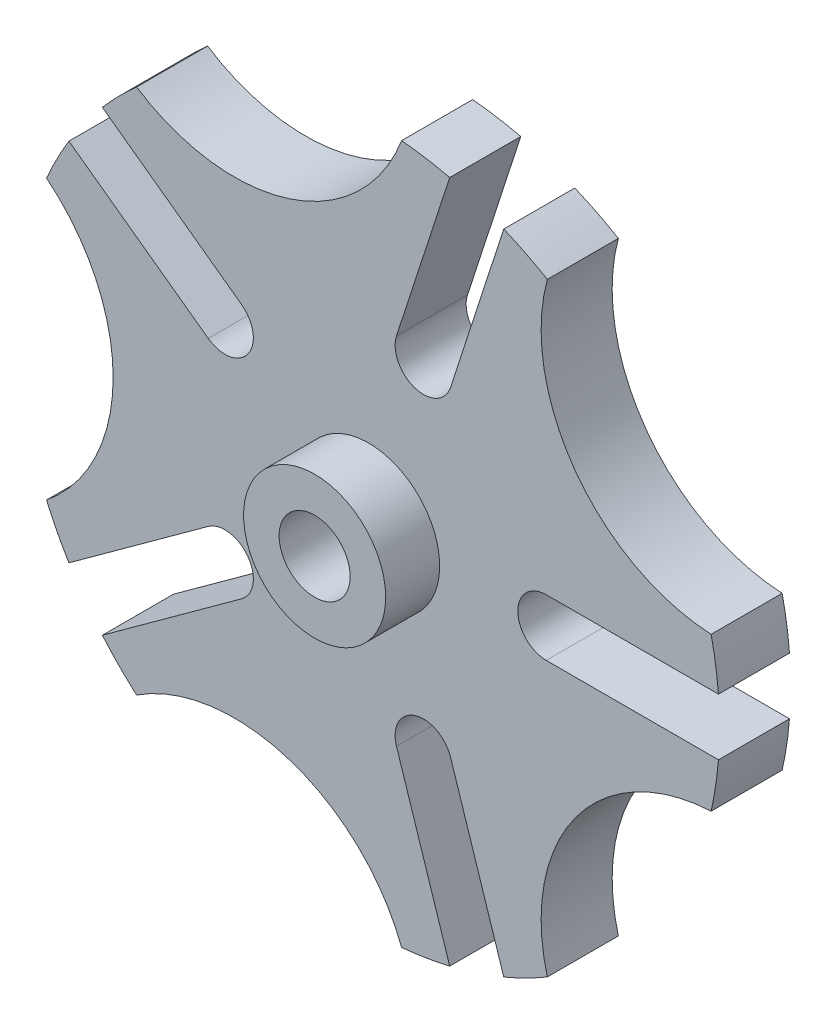
SolidWorks part; units mm, degrees
ref_plane "Front Plane" through (0, 0, 0) normal (0, 0, 1) x (1, 0, 0)
ref_plane "Top Plane" through (0, 0, 0) normal (0, 1, 0) x (1, 0, 0)
ref_plane "Right Plane" through (0, 0, 0) normal (1, 0, 0) x (0, 0, -1)
sketch "Sketch2" plane through (0, 0, 0) normal (0, 0, 1) x (1, 0, 0)
  line L0 (4.1207, 12.6823) -> (0, 0)
  line L1 (0, 0) -> (13.335, 0)
  line L2 (15.875, 2.54) -> (31.266, 2.54)
  line L3 (7.3213, 14.3131) -> (12.0774, 28.9508)
  line L4 (0, 0) -> (18.4736, 13.4218) construction
  arc A0 (31.266, 2.54) -> (30.6129, 6.8459) centre (0, 0) ccw
  arc A1 (4.9056, 15.098) -> (15.6718, 2.5319) centre (0, 0) cw construction
  arc A2 (4.1207, 12.6823) -> (7.3213, 14.3131) centre (4.9056, 15.098) ccw
  arc A3 (15.875, 2.54) -> (13.335, 0) centre (15.875, 0) ccw
  arc A4 (15.9708, 26.9991) -> (30.6129, 6.8459) centre (31.4195, 22.8276) ccw
  arc A5 (15.9708, 26.9991) -> (12.0774, 28.9508) centre (0, 0) ccw
  dimension "D1" = 31.369
  dimension "D3" = 15.875
  dimension "D4" = 5.08
  dimension "D6" = 16.002
  dimension "D2" = 72
  dimension "D5" = 38.8366
extrude "Boss-Extrude1" add sketch "Sketch2" along normal blind 6.35
pattern_circular "CirPattern1" count 5 over 360 about axis through (0, 0, 0) along (0, 0, 1) of "Boss-Extrude1"
sketch "Sketch3" plane through (0, 0, 6.35) normal (0, 0, 1) x (1, 0, 0)
  circle A0 centre (0, 0) radius 6.35
  dimension "D1" = 12.7
extrude "Boss-Extrude2" add sketch "Sketch3" along normal blind 4.826
hole_wizard "1/4 (0.25) Diameter Hole1" positions "Sketch4" profile "Sketch5" hole size "1/4" standard "ANSI Inch" end condition through all
sketch "Sketch4" plane through (0, 0, 11.176) normal (0, 0, 1) x (1, 0, 0)
  point P0 (0, 0)
sketch "Sketch5" plane through (0, 0, 11.176) normal (1, 0, 0) x (0, -1, 0)
  line L0 (0, 0) -> (0, 11.176)
  line L1 (0, 11.176) -> (3.175, 11.176)
  line L2 (3.175, 11.176) -> (3.175, 0)
  line L5 (3.175, 0) -> (0, 0)
  line L11 (0, -6.35) -> (0, 107.95) construction
  dimension "Thru Hole Dia." = 6.35
  dimension "Thru Hole Depth" = 11.176
